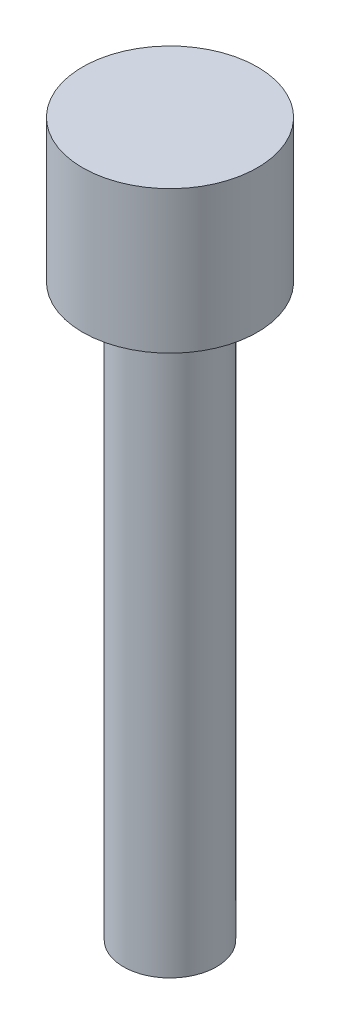
SolidWorks part; units mm, degrees
ref_plane "Front Plane" through (0, 0, 0) normal (0, 0, 1) x (1, 0, 0)
ref_plane "Top Plane" through (0, 0, 0) normal (0, 1, 0) x (1, 0, 0)
ref_plane "Right Plane" through (0, 0, 0) normal (1, 0, 0) x (0, 0, -1)
sketch "Sketch1" plane through (0, 0, 0) normal (0, 1, 0) x (1, 0, 0)
  circle A0 centre (0, 0) radius 1.84
  dimension "D1" = 3.68
extrude "Boss-Extrude1" add sketch "Sketch1" along normal blind 3
sketch "Sketch2" plane through (0, 0, 0) normal (0, -1, 0) x (1, 0, 0)
  circle A0 centre (0, 0) radius 0.98
  dimension "D1" = 1.96
extrude "Boss-Extrude2" add sketch "Sketch2" along normal blind 12
